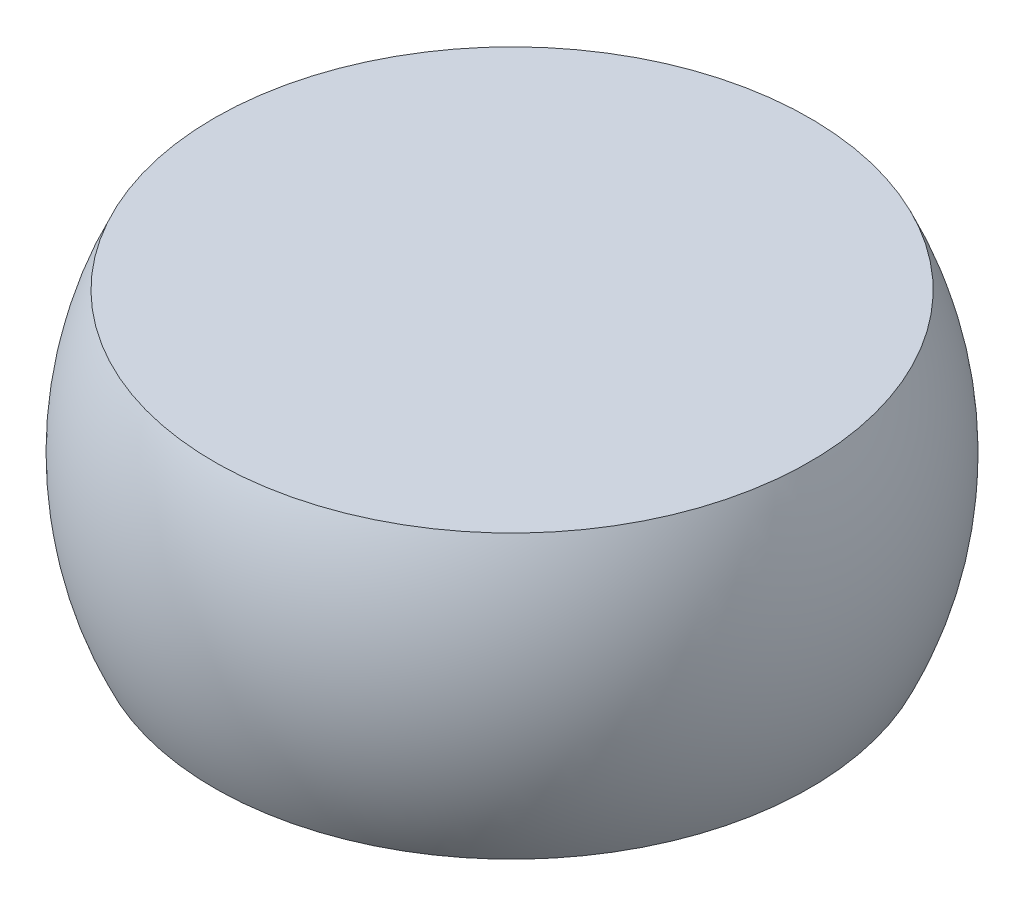
SolidWorks part; units mm, degrees
ref_plane "Front Plane" through (0, 0, 0) normal (0, 0, 1) x (1, 0, 0)
ref_plane "Top Plane" through (0, 0, 0) normal (0, 1, 0) x (1, 0, 0)
ref_plane "Right Plane" through (0, 0, 0) normal (1, 0, 0) x (0, 0, -1)
sketch "Sketch1" plane through (0, 0, 0) normal (0, 0, 1) x (1, 0, 0)
  line L0 (0, 0.15) -> (0, -0.15)
  line L1 (0, 0.15) -> (0.3162, 0.15)
  line L2 (0, -0.15) -> (0.3162, -0.15)
  arc A0 (0.3162, -0.15) -> (0.3162, 0.15) centre (0, 0) ccw
  dimension "D3" = 0.35
  dimension "D1" = 0.15
  dimension "D2" = 0.15
revolve "Revolve1" add sketch "Sketch1" angle 360 about L0
